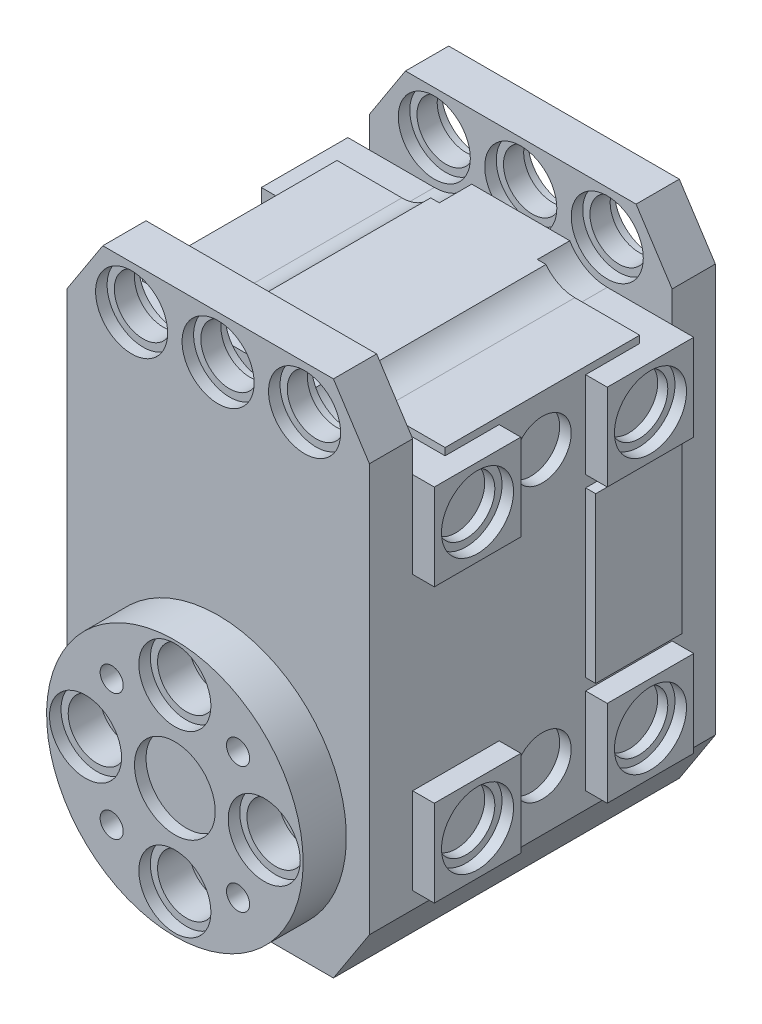
SolidWorks part; units mm, degrees
material "ABS PC"
ref_plane "Front Plane" through (0, 0, 0) normal (0, 0, 1) x (1, 0, 0)
ref_plane "Top Plane" through (0, 0, 0) normal (0, 1, 0) x (1, 0, 0)
ref_plane "Right Plane" through (0, 0, 0) normal (1, 0, 0) x (0, 0, -1)
sketch "Sketch1" plane through (0, 0, 0) normal (0, 0, 1) x (1, 0, 0)
  line L0 (8, 18) -> (-8, 18)
  line L1 (-8, 18) -> (-10.5, 14.15)
  line L2 (-10.5, 14.15) -> (-10.5, -14.15)
  line L3 (-10.5, -14.15) -> (-8, -18)
  line L4 (-8, -18) -> (8, -18)
  line L5 (0, -1000) -> (0, 49000) construction
  line L6 (10.5, -14.15) -> (8, -18)
  line L7 (10.5, 14.15) -> (10.5, -14.15)
  line L8 (8, 18) -> (10.5, 14.15)
  point P2 (-10.5, 0)
  point P10 (0, -18)
  point P14 (0, 18)
  dimension "D1" = 28.3
  dimension "D2" = 2.5
  dimension "D3" = 3.85
  dimension "D4" = 8
extrude "Boss-Extrude1" add sketch "Sketch1" along normal mid plane 24
sketch "Sketch2" plane through (0, 0, 12) normal (0, 0, 1) x (1, 0, 0)
  line L0 (0, -1000) -> (0, 49000) construction
  line L1 (-8, -18) -> (8, -18) construction
  line L2 (-707.1068, -716.2068) -> (34648.2323, 34639.1323) construction
  line L3 (-1000, -9.1) -> (49000, -9.1) construction
  line L4 (707.1068, -716.2068) -> (-34648.2323, 34639.1323) construction
  circle A0 centre (0, -9.1) radius 8.9
  circle A1 centre (0, -15.3) radius 2
  circle A2 centre (0, -9.1) radius 6.2 construction
  circle A3 centre (-4.3841, -13.4841) radius 0.8
  circle A4 centre (4.3841, -13.4841) radius 0.8
  circle A5 centre (6.2, -9.1) radius 2
  circle A6 centre (4.3841, -4.7159) radius 0.8
  circle A7 centre (0, -2.9) radius 2
  circle A8 centre (-4.3841, -4.7159) radius 0.8
  circle A9 centre (-6.2, -9.1) radius 2
  point P24 (0, 0)
  dimension "D1" = 17.8
  dimension "D2" = 4
  dimension "D3" = 0.7
  dimension "D5" = 1.6
  dimension "D4" = 45
  dimension "D6" = 45
extrude "Boss-Extrude2" add sketch "Sketch2" along normal blind 3
sketch "Sketch4" plane through (0, 0, 15) normal (0, 0, 1) x (1, 0, 0)
  circle A0 centre (0, -15.3) radius 2.5
  circle A1 centre (0, -2.9) radius 2.5
  circle A2 centre (-6.2, -9.1) radius 2.5
  circle A3 centre (6.2, -9.1) radius 2.5
  circle A4 centre (0, -9.1) radius 2.8
  point P14 (0, 0)
  point P15 (0, 0)
  dimension "D1" = 5
  dimension "D2" = 5.6
extrude "Cut-Extrude1" cut sketch "Sketch4" against normal blind 0.8
sketch "Sketch9" plane through (0, 0, 12) normal (0, 0, 1) x (1, 0, 0)
  line L0 (0, -1000) -> (0, 49000) construction
  line L5 (8, 18) -> (-8, 18) construction
  circle A0 centre (0, 15) radius 2
  circle A2 centre (6, 15) radius 2
  circle A3 centre (-6, 15) radius 2
  point P9 (0, 0)
  dimension "D1" = 4
  dimension "D2" = 1
  dimension "D3" = 2
extrude "Cut-Extrude4" cut sketch "Sketch9" against normal blind 3
sketch "Sketch10" plane through (0, 0, 12) normal (0, 0, 1) x (1, 0, 0)
  circle A0 centre (0, 15) radius 2.5
  circle A1 centre (6, 15) radius 2.5
  circle A2 centre (-6, 15) radius 2.5
  dimension "D1" = 5
extrude "Cut-Extrude5" cut sketch "Sketch10" against normal blind 0.8
ref_plane "Plane1" through (0, 0, 10.5) normal (0, 0, 1) x (1, 0, 0)
mirror "Mirror2" about plane through (0, 0, 10.5) normal (0, 0, 1) of "Cut-Extrude5"
mirror "Mirror3" about plane through (0, 0, 0) normal (0, 0, 1) of "Cut-Extrude4", "Mirror2", "Cut-Extrude5"
sketch "Sketch8" plane through (0, 0, 0) normal (0, 0, 1) x (1, 0, 0)
  line L0 (8, 18) -> (-8, 18) construction
  line L1 (8, 18) -> (-8, 18)
  line L2 (-8, 18) -> (-10.5, 14.15) construction
  line L3 (-8, 18) -> (-10.5, 14.15)
  line L8 (0, -1000) -> (0, 49000) construction
  line L12 (8, 18) -> (10.5, 14.15)
  line L13 (-10.5, 14.15) -> (-10.5, 12.5)
  line L14 (-10.5, 14.15) -> (-10.5, -14.15) construction
  line L15 (-10.5, 12.5) -> (-6, 12.5)
  line L16 (-4, 13.5) -> (4, 13.5)
  line L18 (10.5, 12.5) -> (6, 12.5)
  line L19 (10.5, 14.15) -> (10.5, 12.5)
  arc A3 (-6, 12.5) -> (-4, 13.5) centre (-6, 15) ccw
  arc A10 (6, 12.5) -> (4, 13.5) centre (6, 15) cw
  point P15 (0, 13.5)
  dimension "D1" = 4
  dimension "D3" = 2.5
  dimension "D2" = 5.5
  dimension "D4" = 4.5
extrude "Cut-Extrude3" cut sketch "Sketch8" against normal mid plane 18
sketch "Sketch5" plane through (10.5, 0, 0) normal (1, 0, 0) x (0, 0, -1)
  line L0 (0, -1000) -> (0, 49000) construction
  line L1 (-9, -7) -> (-3, -7)
  line L2 (-9, -7) -> (-9, -13)
  line L3 (-9, -13) -> (-3, -13)
  line L4 (-3, -7) -> (-3, -13)
  line L5 (-9, -7) -> (-3, -13) construction
  line L6 (-9, -13) -> (-3, -7) construction
  line L7 (3, 5.2) -> (3, -6.2)
  line L9 (-3, 12) -> (-9, 12)
  line L10 (-12, -14.15) -> (-12, 14.15) construction
  line L11 (-3, 12) -> (-3, 6)
  line L12 (-3, 6) -> (-9, 6)
  line L13 (-9, 12) -> (-9, 6)
  line L14 (-3, 12) -> (-9, 6) construction
  line L15 (-3, 6) -> (-9, 12) construction
  line L17 (3, 6) -> (9, 12) construction
  line L18 (3, 12) -> (9, 6) construction
  line L19 (9, -13) -> (3, -7) construction
  line L20 (9, -7) -> (3, -13) construction
  line L21 (9, 12) -> (9, 6)
  line L22 (3, 6) -> (9, 6)
  line L23 (3, 12) -> (3, 6)
  line L24 (3, 12) -> (9, 12)
  line L25 (3, -7) -> (3, -13)
  line L26 (9, -13) -> (3, -13)
  line L27 (9, -7) -> (9, -13)
  line L28 (9, -7) -> (3, -7)
  line L34 (3, -6.2) -> (9, -6.2)
  line L39 (9, -6.2) -> (9, 5.2)
  line L40 (9, 5.2) -> (3, 5.2)
  line L43 (9, 12.5) -> (-9, 12.5) construction
  circle A0 centre (-6, -10) radius 2
  circle A1 centre (6, -10) radius 2
  circle A2 centre (-6, 9) radius 2
  circle A3 centre (6, 9) radius 2
  point P0 (-6, -10)
  point P6 (-6, 9)
  point P28 (6, 9)
  point P29 (6, -10)
  point P33 (0, 0)
  dimension "D5" = 4
  dimension "D1" = 11.4
  dimension "D2" = 6
  dimension "D3" = 6
  dimension "D4" = 3
  dimension "D6" = 0.8
  dimension "D7" = 19
  dimension "D8" = 0.5
extrude "Boss-Extrude3" add sketch "Sketch5" along normal blind 1.5
sketch "Sketch6" plane through (12, 0, 0) normal (1, 0, 0) x (0, 0, -1)
  line L8 (3, -6.2) -> (9, -6.2) construction
  line L9 (9, -6.2) -> (9, 5.2) construction
  line L10 (9, 5.2) -> (3, 5.2) construction
  line L11 (3, 5.2) -> (3, -6.2) construction
  line L12 (3, -6.2) -> (9, -6.2)
  line L13 (9, -6.2) -> (9, 5.2)
  line L14 (9, 5.2) -> (3, 5.2)
  line L15 (3, 5.2) -> (3, -6.2)
  circle A0 centre (-6, -10) radius 2.5
  circle A4 centre (-6, 9) radius 2.5
  circle A5 centre (6, 9) radius 2.5
  circle A6 centre (6, -10) radius 2.5
  dimension "D1" = 5
extrude "Cut-Extrude2" cut sketch "Sketch6" against normal blind 0.8
sketch "Sketch11" plane through (10.5, 0, 0) normal (1, 0, 0) x (0, 0, -1)
  circle A0 centre (0, 9) radius 2
  circle A1 centre (-6, 9) radius 2 construction
  circle A2 centre (-6, 9) radius 2 construction
  circle A3 centre (0, -10) radius 2
  circle A4 centre (-6, -10) radius 2
  circle A5 centre (-6, -10) radius 2 construction
  point P2 (0, 0)
  point P3 (0, 0)
  dimension "D1" = 4
  dimension "D2" = 0
extrude "Cut-Extrude6" cut sketch "Sketch11" against normal blind 0.8
mirror "Mirror4" about plane through (0, 0, 0) normal (1, 0, 0) of "Cut-Extrude6", "Boss-Extrude3", "Cut-Extrude2"
sketch "Sketch12" plane through (0, 0, 9) normal (0, 0, -1) x (-1, 0, 0)
  line L0 (-6, 12.5) -> (-10.5, 12.5) construction
  line L1 (-6, 12.5) -> (-10.5, 12.5)
  line L2 (-10.5, 12.5) -> (-10.5, 12)
  line L3 (-10.5, 12) -> (-6, 12)
  line L4 (-2, 13.5) -> (-4, 13.5) construction
  line L6 (0, -1000) -> (0, 49000) construction
  line L7 (3.4019, 13.5) -> (4, 13.5)
  line L8 (6, 12.5) -> (10.5, 12.5)
  line L9 (10.5, 12) -> (6, 12)
  line L10 (-3.4019, 13.5) -> (-4, 13.5)
  line L11 (10.5, 12) -> (10.5, 12.5)
  arc A0 (-6, 12) -> (-3.4019, 13.5) centre (-6, 15) ccw
  arc A1 (-6, 12.5) -> (-4, 13.5) centre (-6, 15) ccw
  arc A2 (6, 12) -> (3.4019, 13.5) centre (6, 15) cw
  arc A3 (6, 12.5) -> (4, 13.5) centre (6, 15) cw
  dimension "D1" = 0.5
extrude "Cut-Extrude7" cut sketch "Sketch12" along normal blind 2.25
mirror "Mirror5" about plane through (0, 0, 0) normal (0, 0, 1) of "Cut-Extrude7"
sketch "Sketch13" plane through (0, 0, -12) normal (0, 0, -1) x (-1, 0, 0)
  line L0 (8, -18) -> (-8, -18) construction
  circle A0 centre (0, -9.1) radius 2
  circle A1 centre (6, -9.1) radius 2
  circle A2 centre (-6, -9.1) radius 2
  point P6 (0, 0)
  point P7 (0, 0)
  dimension "D1" = 4
  dimension "D2" = 2
  dimension "D3" = 2
  dimension "D4" = 8.9
extrude "Cut-Extrude8" cut sketch "Sketch13" against normal blind 3
sketch "Sketch14" plane through (0, 0, -12) normal (0, 0, -1) x (-1, 0, 0)
  circle A0 centre (0, -9.1) radius 2.5
  circle A1 centre (6, -9.1) radius 2.5
  circle A2 centre (-6, -9.1) radius 2.5
  dimension "D1" = 5
extrude "Cut-Extrude9" cut sketch "Sketch14" against normal blind 0.8
